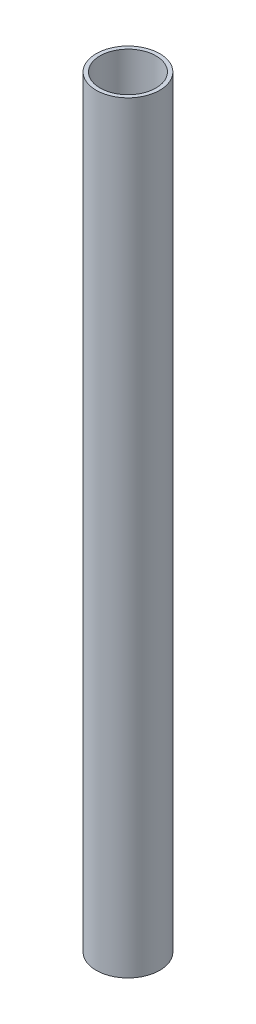
SolidWorks part; units mm, degrees
ref_plane "Front" through (0, 0, 0) normal (0, 0, 1) x (1, 0, 0)
ref_plane "Top" through (0, 0, 0) normal (0, 1, 0) x (1, 0, 0)
ref_plane "Right" through (0, 0, 0) normal (1, 0, 0) x (0, 0, -1)
sketch "Sketch1" plane through (0, 0, 0) normal (0, 1, 0) x (1, 0, 0)
  circle A0 centre (0, 0) radius 6.35
  circle A1 centre (0, 0) radius 5.588
  dimension "D1" = 12.7
  dimension "D2" = 0.762
extrude "Boss-Extrude1" add sketch "Sketch1" along normal blind 152.4
